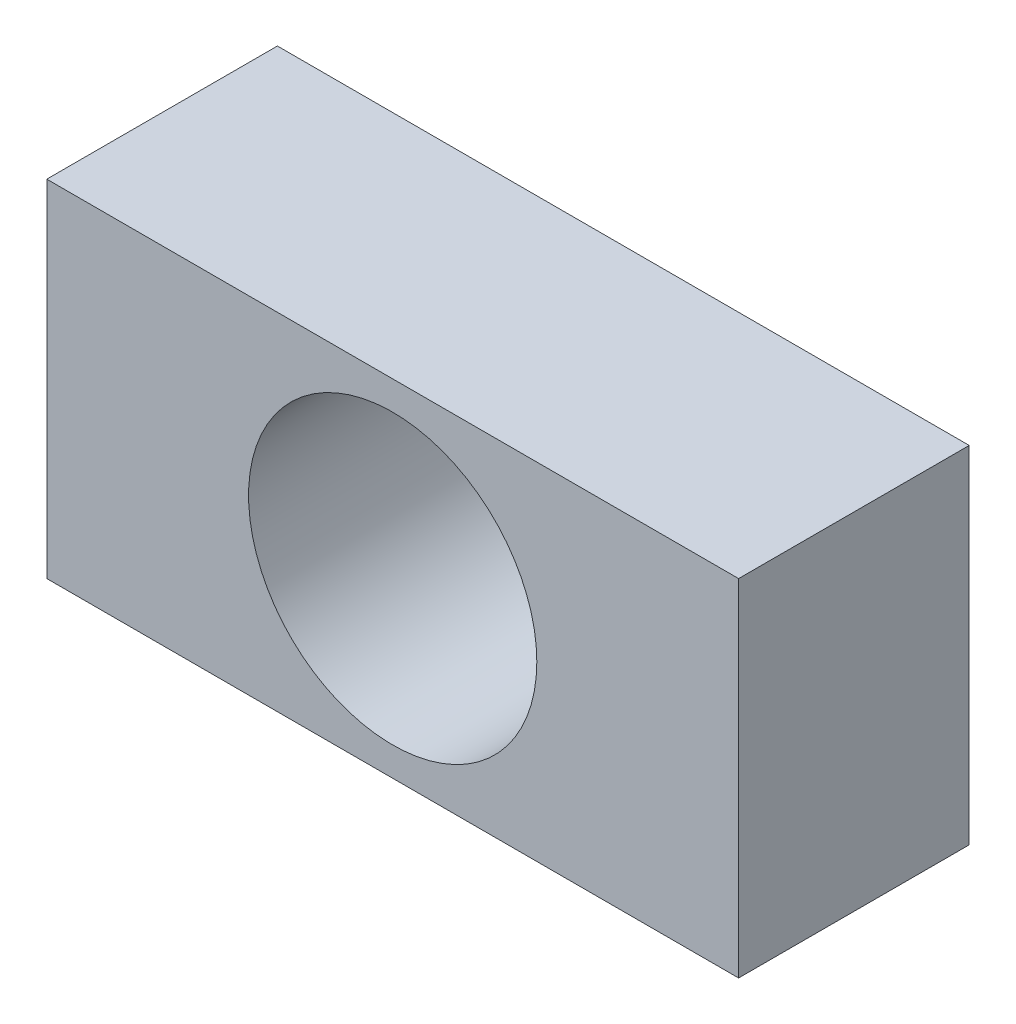
SolidWorks part; units mm, degrees
ref_plane "Front Plane" through (0, 0, 0) normal (0, 0, 1) x (1, 0, 0)
ref_plane "Top Plane" through (0, 0, 0) normal (0, 1, 0) x (1, 0, 0)
ref_plane "Right Plane" through (0, 0, 0) normal (1, 0, 0) x (0, 0, -1)
sketch "Sketch1" plane through (0, 0, 0) normal (0, 0, 1) x (1, 0, 0)
  line L1 (-27.4286, 18) -> (32.5714, 18)
  line L2 (-27.4286, 18) -> (-27.4286, -12)
  line L3 (-27.4286, -12) -> (32.5714, -12)
  line L4 (32.5714, 18) -> (32.5714, -12)
  circle A0 centre (2.5714, 3) radius 12.5
  dimension "D3" = 25
  dimension "D1" = 60
  dimension "D2" = 30
  dimension "D4" = 15
extrude "Boss-Extrude2" add sketch "Sketch1" along normal blind 20
sketch "Sketch2" plane through (0, -12, 0) normal (0, -1, 0) x (1, 0, 0)
  circle A0 centre (-20.4286, 10) radius 4
  circle A1 centre (25.5714, 10) radius 4
extrude "Cut-Extrude1" cut sketch "Sketch2" against normal blind 10
